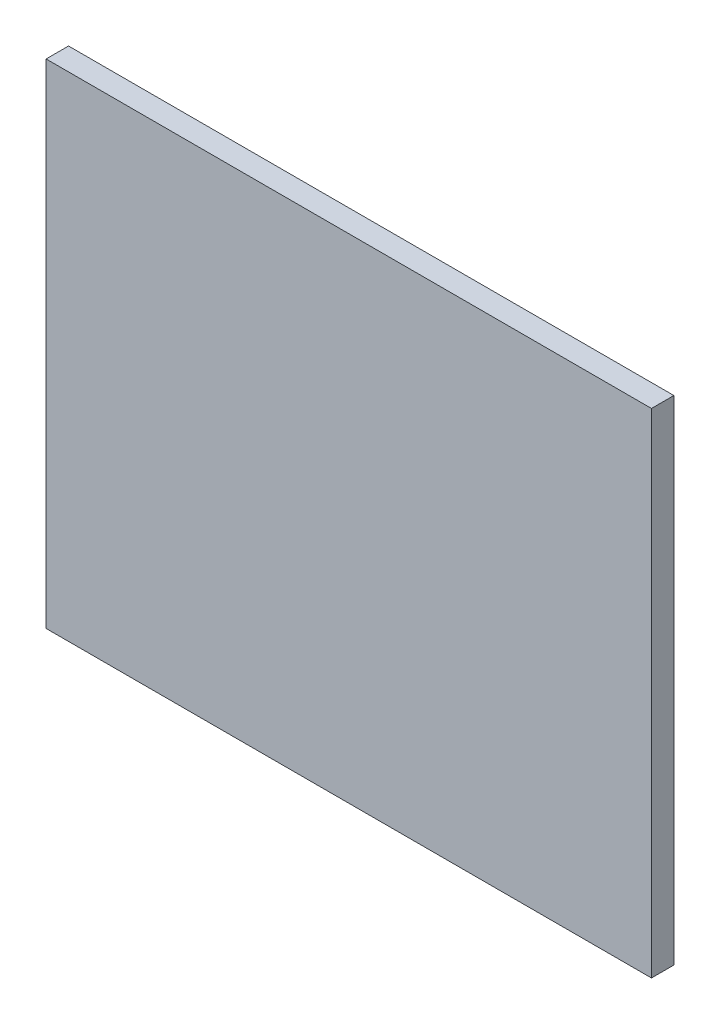
SolidWorks part; units mm, degrees
ref_plane "Plano frontal" through (0, 0, 0) normal (0, 0, 1) x (1, 0, 0)
ref_plane "Plano superior" through (0, 0, 0) normal (0, 1, 0) x (1, 0, 0)
ref_plane "Plano direito" through (0, 0, 0) normal (1, 0, 0) x (0, 0, -1)
sketch "Esboço1" plane through (0, 0, 0) normal (0, 0, 1) x (1, 0, 0)
  line L1 (0, 0) -> (-27, 0)
  line L2 (0, 0) -> (0, 22)
  line L3 (0, 22) -> (-27, 22)
  line L4 (-27, 0) -> (-27, 22)
extrude "Ressalto-extrusão1" add sketch "Esboço1" along normal blind 1
